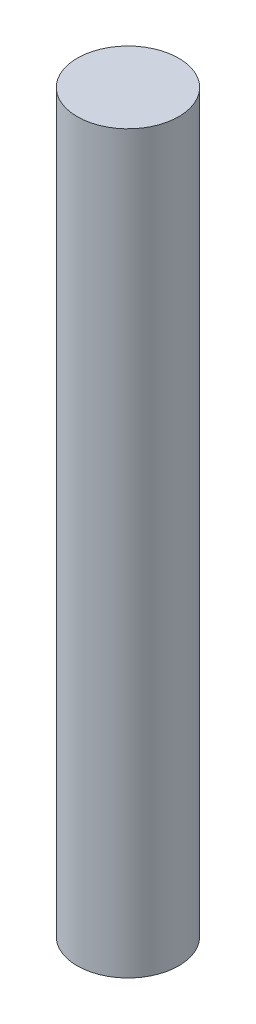
SolidWorks part; units mm, degrees
ref_plane "Front Plane" through (0, 0, 0) normal (0, 0, 1) x (1, 0, 0)
ref_plane "Top Plane" through (0, 0, 0) normal (0, 1, 0) x (1, 0, 0)
ref_plane "Right Plane" through (0, 0, 0) normal (1, 0, 0) x (0, 0, -1)
sketch "Sketch1" plane through (0, 0, 0) normal (0, 1, 0) x (1, 0, 0)
  circle A0 centre (0, 0) radius 1
  dimension "D1" = 2
extrude "Boss-Extrude1" add sketch "Sketch1" along normal blind 14.5
